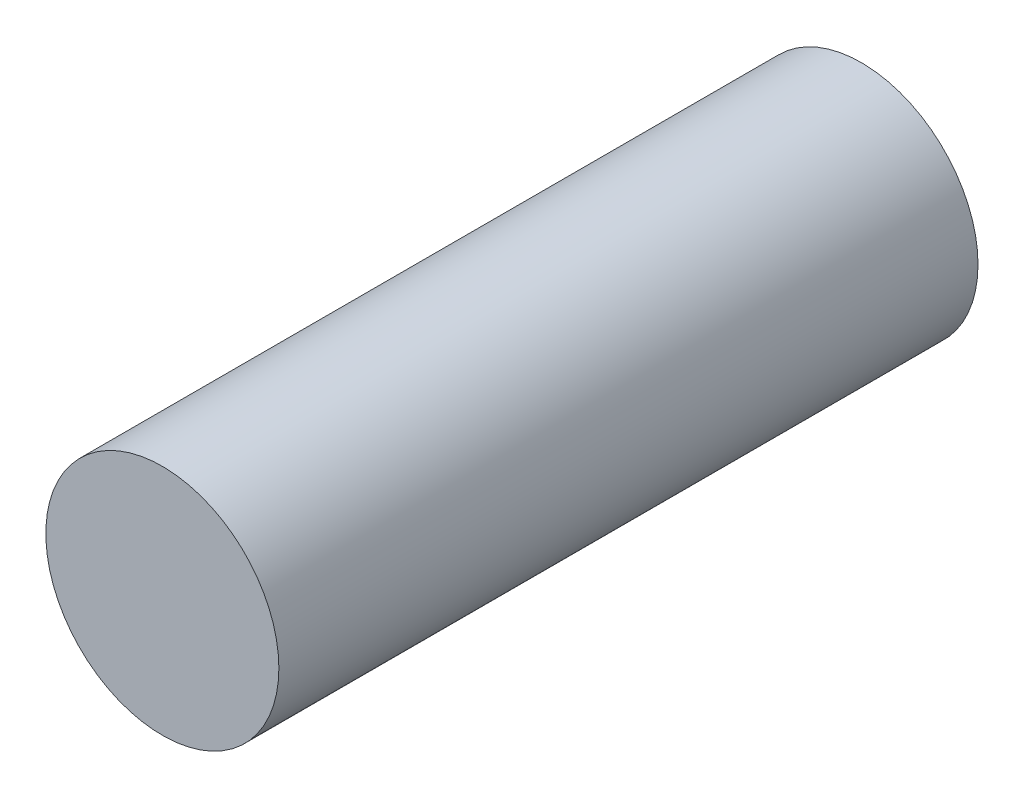
SolidWorks part; units mm, degrees
ref_plane "前视基准面" through (0, 0, 0) normal (0, 0, 1) x (1, 0, 0)
ref_plane "上视基准面" through (0, 0, 0) normal (0, 1, 0) x (1, 0, 0)
ref_plane "右视基准面" through (0, 0, 0) normal (1, 0, 0) x (0, 0, -1)
sketch "草图1" plane through (0, 0, 0) normal (0, 0, 1) x (1, 0, 0)
  circle A0 centre (0, 0) radius 5
  dimension "D1" = 10
extrude "凸台-拉伸1" add sketch "草图1" along normal blind 30
